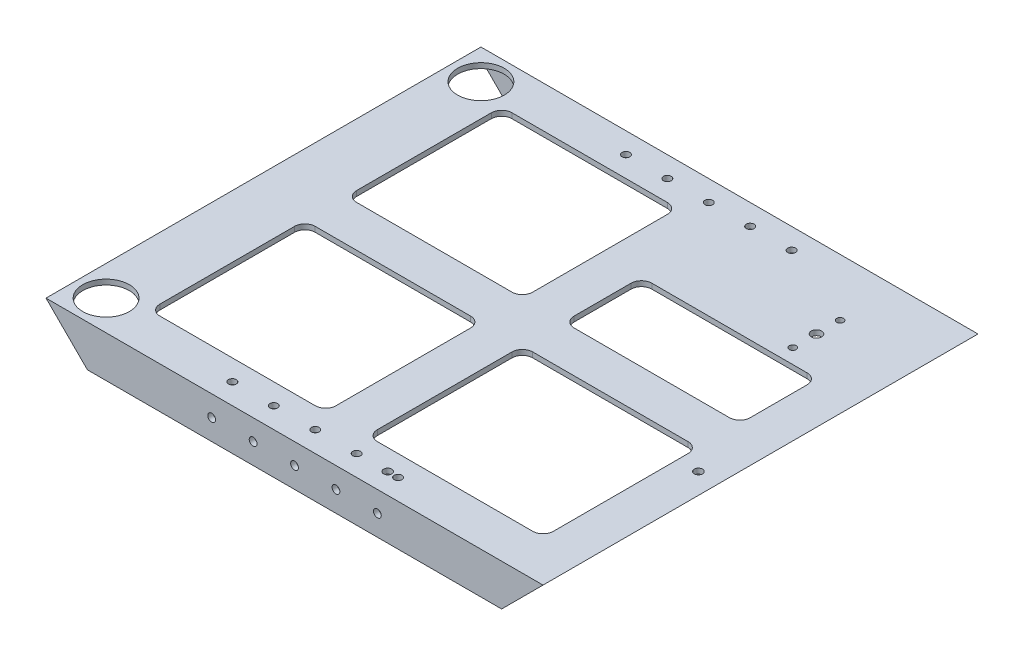
SolidWorks part; units mm, degrees
ref_plane "Front Plane" through (0, 0, 0) normal (0, 0, 1) x (1, 0, 0)
ref_plane "Top Plane" through (0, 0, 0) normal (0, 1, 0) x (1, 0, 0)
ref_plane "Right Plane" through (0, 0, 0) normal (1, 0, 0) x (0, 0, -1)
sketch "Sketch2" plane through (0, 0, 0) normal (0, 1, 0) x (1, 0, 0)
  line L1 (0, 0) -> (304.8, 0)
  line L2 (0, 0) -> (0, 266.7)
  line L3 (0, 266.7) -> (304.8, 266.7)
  line L4 (304.8, 0) -> (304.8, 266.7)
  dimension "D1" = 304.8
  dimension "D2" = 266.7
extrude "Boss-Extrude1" add sketch "Sketch2" along normal blind 25.4
sketch "Sketch12" plane through (304.8, 0, 0) normal (1, 0, 0) x (0, 0, -1)
  line L0 (0, 0) -> (266.7, 0) construction
  line L1 (3.175, 0) -> (263.525, 0)
  line L2 (3.175, 0) -> (3.175, 22.225)
  line L3 (3.175, 22.225) -> (263.525, 22.225)
  line L4 (263.525, 0) -> (263.525, 22.225)
  line L5 (0, 25.4) -> (266.7, 25.4) construction
  line L6 (0, 25.4) -> (0, 0) construction
  line L7 (266.7, 25.4) -> (266.7, 0) construction
  dimension "D1" = 3.175
  dimension "D2" = 3.175
  dimension "D3" = 3.175
extrude "Cut-Extrude8" cut sketch "Sketch12" against normal through all
sketch "Sketch13" plane through (0, 0, 0) normal (0, 0, 1) x (1, 0, 0)
  line L0 (304.8, 25.4) -> (279.4, 0)
  line L1 (0, 0) -> (304.8, 0) construction
  line L2 (279.4, 0) -> (304.8, 0)
  line L3 (304.8, 0) -> (304.8, 25.4)
  line L4 (152.4, 25.4) -> (152.4, 0) construction
  line L5 (0, 25.4) -> (304.8, 25.4) construction
  line L6 (0, 0) -> (0, 25.4)
  line L7 (25.4, 0) -> (0, 0)
  line L8 (0, 25.4) -> (25.4, 0)
  dimension "D1" = 45
extrude "Cut-Extrude9" cut sketch "Sketch13" against normal through all
sketch "Sketch14" plane through (0, 22.225, 0) normal (0, -1, 0) x (1, 0, 0)
  line L0 (0, -133.35) -> (304.8, -133.35) construction
  line L1 (0, -266.7) -> (0, 0) construction
  line L2 (304.8, 0) -> (304.8, -266.7) construction
  line L3 (3.175, -3.175) -> (301.625, -3.175) construction
  line L4 (3.175, -3.175) -> (3.175, -263.525) construction
  line L5 (25.4, -263.525) -> (279.4, -263.525) construction
  line L6 (301.625, -263.525) -> (301.625, -3.175) construction
  circle A0 centre (18.415, -18.415) radius 14.2875
  circle A1 centre (18.415, -248.285) radius 14.2875
  circle A2 centre (255.27, -217.17) radius 3.175
  dimension "D3" = 28.575
  dimension "D4" = 6.35
  dimension "D1" = 15.24
  dimension "D2" = 15.24
  dimension "D5" = 46.355
  dimension "D6" = 46.355
extrude "Cut-Extrude10" cut sketch "Sketch14" against normal through all
sketch "Sketch15" plane through (0, 25.4, 0) normal (0, 1, 0) x (1, 0, 0)
  line L0 (304.8, 266.7) -> (0, 266.7) construction
  line L1 (44.45, 241.3) -> (139.7, 241.3)
  line L2 (38.1, 234.95) -> (38.1, 152.4)
  line L3 (44.45, 146.05) -> (139.7, 146.05)
  line L4 (146.05, 234.95) -> (146.05, 152.4)
  line L5 (44.45, 120.65) -> (139.7, 120.65)
  line L6 (38.1, 114.3) -> (38.1, 31.75)
  line L7 (44.45, 25.4) -> (139.7, 25.4)
  line L8 (146.05, 114.3) -> (146.05, 31.75)
  line L9 (177.8, 193.675) -> (273.05, 193.675)
  line L10 (171.45, 187.325) -> (171.45, 152.4)
  line L11 (177.8, 146.05) -> (273.05, 146.05)
  line L12 (279.4, 187.325) -> (279.4, 152.4)
  line L13 (177.8, 120.65) -> (273.05, 120.65)
  line L14 (171.45, 114.3) -> (171.45, 31.75)
  line L15 (177.8, 25.4) -> (273.05, 25.4)
  line L16 (279.4, 114.3) -> (279.4, 31.75)
  line L17 (0, 0) -> (304.8, 0) construction
  line L18 (0, 266.7) -> (0, 0) construction
  line L19 (304.8, 0) -> (304.8, 266.7) construction
  arc A0 (139.7, 25.4) -> (146.05, 31.75) centre (139.7, 31.75) ccw
  arc A1 (38.1, 31.75) -> (44.45, 25.4) centre (44.45, 31.75) ccw
  arc A2 (44.45, 120.65) -> (38.1, 114.3) centre (44.45, 114.3) ccw
  arc A3 (139.7, 120.65) -> (146.05, 114.3) centre (139.7, 114.3) cw
  arc A4 (273.05, 25.4) -> (279.4, 31.75) centre (273.05, 31.75) ccw
  arc A5 (171.45, 31.75) -> (177.8, 25.4) centre (177.8, 31.75) ccw
  arc A6 (177.8, 120.65) -> (171.45, 114.3) centre (177.8, 114.3) ccw
  arc A7 (273.05, 120.65) -> (279.4, 114.3) centre (273.05, 114.3) cw
  arc A8 (273.05, 193.675) -> (279.4, 187.325) centre (273.05, 187.325) cw
  arc A9 (273.05, 146.05) -> (279.4, 152.4) centre (273.05, 152.4) ccw
  arc A10 (171.45, 152.4) -> (177.8, 146.05) centre (177.8, 152.4) ccw
  arc A11 (177.8, 193.675) -> (171.45, 187.325) centre (177.8, 187.325) ccw
  arc A12 (139.7, 241.3) -> (146.05, 234.95) centre (139.7, 234.95) cw
  arc A13 (139.7, 146.05) -> (146.05, 152.4) centre (139.7, 152.4) ccw
  arc A14 (38.1, 152.4) -> (44.45, 146.05) centre (44.45, 152.4) ccw
  arc A15 (44.45, 241.3) -> (38.1, 234.95) centre (44.45, 234.95) ccw
  point P56 (146.05, 193.675)
  dimension "D1" = 6.35
  dimension "D2" = 25.4
  dimension "D3" = 25.4
  dimension "D4" = 38.1
  dimension "D5" = 25.4
  dimension "D6" = 25.4
  dimension "D7" = 25.4
extrude "Cut-Extrude11" cut sketch "Sketch15" against normal blind 3.175
sketch "Sketch16" plane through (0, 0, 0) normal (0, 0, 1) x (1, 0, 0)
  line L0 (12.7, 12.7) -> (292.1, 12.7) construction
  line L1 (25.4, 0) -> (0, 25.4) construction
  line L2 (304.8, 25.4) -> (279.4, 0) construction
  circle A0 centre (152.4, 12.7) radius 2.3813
  circle A1 centre (127, 12.7) radius 2.3813
  circle A2 centre (101.6, 12.7) radius 2.3813
  circle A3 centre (177.8, 12.7) radius 2.3813
  circle A4 centre (203.2, 12.7) radius 2.3813
  dimension "D1" = 4.7625
  dimension "D2" = 25.4
  dimension "D3" = 25.4
  dimension "D4" = 25.4
  dimension "D5" = 25.4
extrude "Cut-Extrude12" cut sketch "Sketch16" against normal through all
sketch "Sketch17" plane through (0, 25.4, 0) normal (0, 1, 0) x (1, 0, 0)
  line L0 (304.8, 12.7) -> (0, 12.7) construction
  line L1 (0, 266.7) -> (0, 0) construction
  line L2 (304.8, 0) -> (304.8, 266.7) construction
  line L3 (0, 0) -> (304.8, 0) construction
  line L4 (0, 133.35) -> (304.8, 133.35) construction
  circle A0 centre (152.4, 12.7) radius 2.3813
  circle A1 centre (177.8, 12.7) radius 2.3813
  circle A2 centre (203.2, 12.7) radius 2.3813
  circle A3 centre (127, 12.7) radius 2.3813
  circle A4 centre (101.6, 12.7) radius 2.3813
  circle A5 centre (203.2, 254) radius 2.3812
  circle A6 centre (177.8, 254) radius 2.3813
  circle A7 centre (152.4, 254) radius 2.3813
  circle A8 centre (127, 254) radius 2.3812
  circle A9 centre (101.6, 254) radius 2.3812
  dimension "D3" = 25.4
  dimension "D4" = 25.4
  dimension "D5" = 25.4
  dimension "D2" = 4.7625
  dimension "D1" = 12.7
  dimension "D6" = 25.4
extrude "Cut-Extrude13" cut sketch "Sketch17" against normal through all
sketch "Sketch18" plane through (0, 25.4, 0) normal (0, 1, 0) x (1, 0, 0)
  circle A0 centre (255.27, 217.17) radius 14.5034 construction
  circle A1 centre (255.27, 217.17) radius 3.175 construction
  circle A2 centre (255.27, 231.6734) radius 2.0955
  circle A3 centre (255.27, 202.6666) radius 2.0955
  dimension "D1" = 29.0068
  dimension "D2" = 4.191
extrude "Cut-Extrude14" cut sketch "Sketch18" against normal blind 3.175
sketch "Sketch19" plane through (0, 25.4, 0) normal (0, 1, 0) x (1, 0, 0)
  line L0 (304.8, 0) -> (304.8, 266.7) construction
  line L1 (177.8, 25.4) -> (273.05, 25.4) construction
  circle A0 centre (196.85, 12.7) radius 2.54
  dimension "D1" = 107.95
  dimension "D2" = 5.08
  dimension "D3" = 12.7
extrude "Cut-Extrude15" cut sketch "Sketch19" against normal through all
sketch "Sketch20" plane through (0, 25.4, 0) normal (0, 1, 0) x (1, 0, 0)
  line L0 (279.4, 31.75) -> (279.4, 114.3) construction
  circle A0 centre (292.1, 107.95) radius 2.54
  dimension "D1" = 107.95
  dimension "D2" = 12.7
  dimension "D3" = 5.08
extrude "Cut-Extrude16" cut sketch "Sketch20" against normal through all
equation "\"D3@Sketch16\"=\"D2@Sketch16\""
equation "\"D4@Sketch16\"=\"D2@Sketch16\""
equation "\"D5@Sketch16\"=\"D2@Sketch16\""
equation "\"D4@Sketch17\"=\"D3@Sketch17\""
equation "\"D5@Sketch17\"=\"D3@Sketch17\""
equation "\"D6@Sketch17\"=\"D3@Sketch17\""
